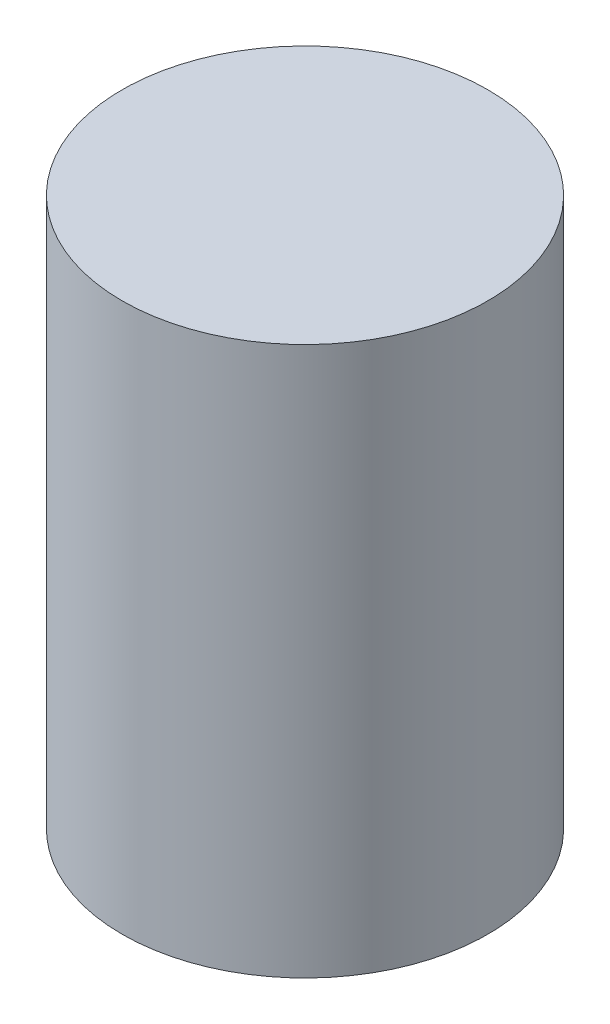
SolidWorks part; units mm, degrees
ref_plane "Front Plane" through (0, 0, 0) normal (0, 0, 1) x (1, 0, 0)
ref_plane "Top Plane" through (0, 0, 0) normal (0, 1, 0) x (1, 0, 0)
ref_plane "Right Plane" through (0, 0, 0) normal (1, 0, 0) x (0, 0, -1)
sketch "Sketch1" plane through (0, 0, 0) normal (0, 1, 0) x (1, 0, 0)
  circle A0 centre (0, 0) radius 5
  dimension "D1" = 10
extrude "Boss-Extrude1" add sketch "Sketch1" along normal blind 15
